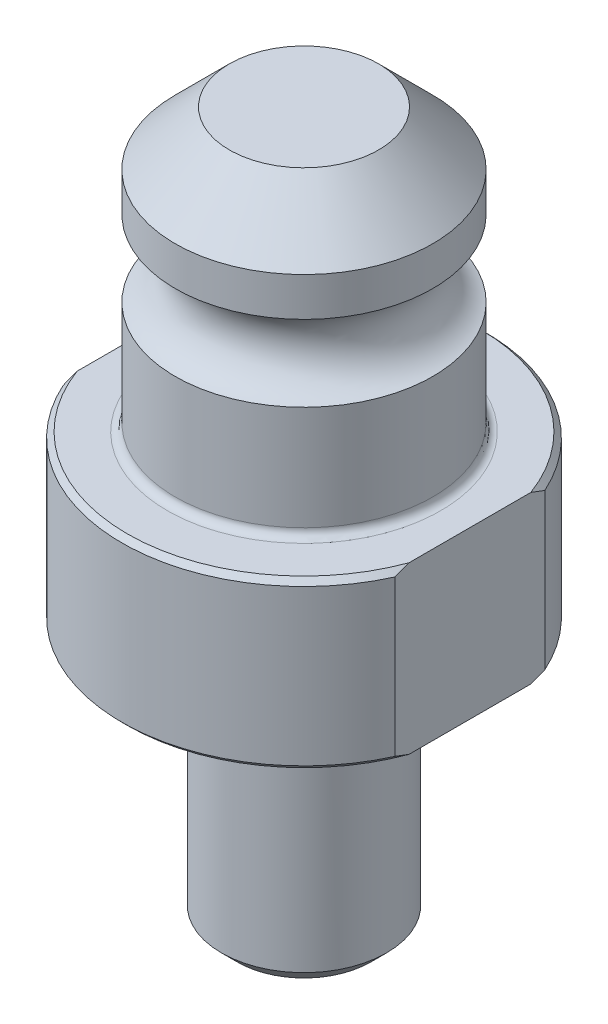
SolidWorks part; units mm, degrees
ref_plane "Front Plane" through (0, 0, 0) normal (0, 0, 1) x (1, 0, 0)
ref_plane "Top Plane" through (0, 0, 0) normal (0, 1, 0) x (1, 0, 0)
ref_plane "Right Plane" through (0, 0, 0) normal (1, 0, 0) x (0, 0, -1)
sketch "Sketch1" plane through (0, 0, 0) normal (0, 0, 1) x (1, 0, 0)
  line L0 (0, 43.0022) -> (0, -24.9936)
  line L1 (0, -24.9936) -> (-7.9375, -24.9936)
  line L2 (-7.9375, -24.9936) -> (-7.9375, -3.81)
  line L3 (-7.9375, -3.81) -> (-6.223, -3.81)
  line L4 (-6.223, -3.81) -> (-6.223, -1.27)
  line L5 (-7.493, 0) -> (-17.5006, 0)
  line L6 (-17.5006, 0) -> (-17.5006, 15.9512)
  line L7 (-17.5006, 15.9512) -> (-12.3825, 15.9512)
  line L8 (-12.3825, 15.9512) -> (-12.3825, 26.7462)
  line L9 (-12.3825, 37.7952) -> (-7.1755, 43.0022)
  line L10 (-7.1755, 43.0022) -> (0, 43.0022)
  line L11 (0, -24.9936) -> (0, -73.6863) construction
  line L12 (-12.3825, 34.0614) -> (-12.3825, 37.7952)
  arc A0 (-12.3825, 26.7462) -> (-12.3825, 34.0614) centre (-13.467, 30.4038) ccw
  arc A1 (-7.493, 0) -> (-6.223, -1.27) centre (-7.493, -1.27) cw
  dimension "D13" = 19.304
  dimension "D14" = 1.27
  dimension "D1" = 15.875
  dimension "D2" = 12.446
  dimension "D3" = 35.0012
  dimension "D4" = 24.765
  dimension "D5" = 24.9936
  dimension "D6" = 15.9512
  dimension "D7" = 3.81
  dimension "D8" = 45
  dimension "D9" = 14.351
  dimension "D10" = 43.0022
  dimension "D11" = 10.795
  dimension "D12" = 7.3152
revolve "Revolve1" add sketch "Sketch1" angle 360 about L11
chamfer "Chamfer1" distance 0.508 angle 45 2 edges at (-17.5006, 0, 0) (-17.5006, 15.9512, 0)
chamfer "Chamfer2" distance 1.524 angle 45 1 edges at (-7.9375, -24.9936, 0)
sketch "Sketch2" plane through (0, 15.9512, 0) normal (0, 1, 0) x (1, 0, 0)
  line L0 (-15.9512, 7.1993) -> (-15.9512, -7.1993)
  line L1 (15.9512, 7.1993) -> (15.9512, -7.1993)
  circle A0 centre (0, 0) radius 17.5006 construction
  arc A1 (15.9512, -7.1993) -> (15.9512, 7.1993) centre (0, 0) ccw
  arc A2 (-15.9512, 7.1993) -> (-15.9512, -7.1993) centre (0, 0) ccw
  dimension "D1" = 15.9512
  dimension "D2" = 15.9512
extrude "Cut-Extrude1" cut sketch "Sketch2" against normal through all
fillet "Fillet1" radius 0.762 1 edges at (-12.3825, 15.9512, 0)
